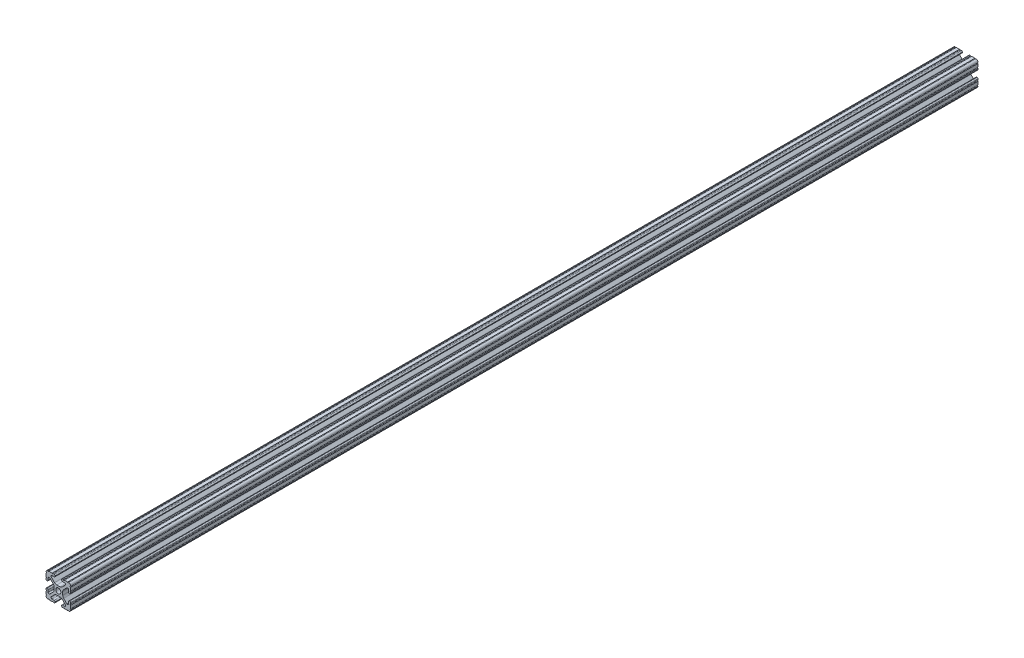
SolidWorks part; units mm, degrees
ref_plane "Front Plane" through (0, 0, 0) normal (0, 0, 1) x (1, 0, 0)
ref_plane "Top Plane" through (0, 0, 0) normal (0, 1, 0) x (1, 0, 0)
ref_plane "Right Plane" through (0, 0, 0) normal (1, 0, 0) x (0, 0, -1)
sketch "Sketch1" plane through (0, 0, 0) normal (0, 0, 1) x (1, 0, 0)
  line L88 (-7.1797, -8.6452) -> (-3.9523, -5.4237)
  line L89 (-1.7093, -4.4958) -> (1.7093, -4.4958)
  line L90 (3.9523, -5.4237) -> (7.1797, -8.6452)
  line L91 (6.4164, -10.4902) -> (4.2875, -10.4902)
  line L92 (3.2385, -11.5392) -> (3.2385, -11.651)
  line L93 (4.2875, -12.7) -> (5.3171, -12.7)
  line L94 (6.3331, -12.7) -> (9.5504, -12.7)
  line L95 (12.7, -9.5504) -> (12.7, -6.3331)
  line L96 (12.7, -5.3171) -> (12.7, -4.2875)
  line L97 (11.651, -3.2385) -> (11.5392, -3.2385)
  line L98 (10.4902, -4.2875) -> (10.4902, -6.4021)
  line L99 (8.7371, -7.1294) -> (5.441, -3.8408)
  line L100 (4.5085, -1.5932) -> (4.5085, 1.5932)
  line L101 (5.441, 3.8408) -> (8.7371, 7.1294)
  line L102 (10.4902, 6.4021) -> (10.4902, 4.2875)
  line L103 (11.5392, 3.2385) -> (11.651, 3.2385)
  line L104 (12.7, 4.2875) -> (12.7, 5.3171)
  line L105 (12.7, 6.3331) -> (12.7, 9.5504)
  line L106 (9.5504, 12.7) -> (6.3331, 12.7)
  line L107 (5.3171, 12.7) -> (4.2875, 12.7)
  line L108 (3.2385, 11.651) -> (3.2385, 11.5392)
  line L109 (4.2875, 10.4902) -> (6.4768, 10.4902)
  line L110 (7.207, 8.7244) -> (3.8983, 5.4232)
  line L111 (1.6558, 4.4958) -> (-1.6558, 4.4958)
  line L112 (-3.8983, 5.4232) -> (-7.207, 8.7244)
  line L113 (-6.4768, 10.4902) -> (-4.2875, 10.4902)
  line L114 (-3.2385, 11.5392) -> (-3.2385, 11.651)
  line L115 (-4.2875, 12.7) -> (-5.3171, 12.7)
  line L116 (-6.3331, 12.7) -> (-9.5504, 12.7)
  line L117 (-12.7, 9.5504) -> (-12.7, 6.3331)
  line L118 (-12.7, 5.3171) -> (-12.7, 4.2875)
  line L119 (-11.651, 3.2385) -> (-11.5392, 3.2385)
  line L120 (-10.4902, 4.2875) -> (-10.4902, 6.4021)
  line L121 (-8.7371, 7.1294) -> (-5.441, 3.8408)
  line L122 (-4.5085, 1.5932) -> (-4.5085, -1.5932)
  line L123 (-5.441, -3.8408) -> (-8.7371, -7.1294)
  line L124 (-10.4902, -6.4021) -> (-10.4902, -4.2875)
  line L125 (-11.5392, -3.2385) -> (-11.651, -3.2385)
  line L126 (-12.7, -4.2875) -> (-12.7, -5.3171)
  line L127 (-12.7, -6.3331) -> (-12.7, -9.5504)
  line L128 (-9.5504, -12.7) -> (-6.3331, -12.7)
  line L129 (-5.3171, -12.7) -> (-4.2875, -12.7)
  line L130 (-3.2385, -11.651) -> (-3.2385, -11.5392)
  line L131 (-4.2875, -10.4902) -> (-6.4164, -10.4902)
  circle A1 centre (0, 0) radius 2.6035
  arc A104 (-7.1797, -8.6452) -> (-6.4164, -10.4902) centre (-6.4164, -9.4098) ccw
  arc A105 (-1.7093, -4.4958) -> (-3.9523, -5.4237) centre (-1.7093, -7.6708) ccw
  arc A106 (3.9523, -5.4237) -> (1.7093, -4.4958) centre (1.7093, -7.6708) ccw
  arc A107 (6.4164, -10.4902) -> (7.1797, -8.6452) centre (6.4164, -9.4098) ccw
  arc A108 (4.2875, -10.4902) -> (3.2385, -11.5392) centre (4.2875, -11.5392) ccw
  arc A109 (3.2385, -11.651) -> (4.2875, -12.7) centre (4.2875, -11.651) ccw
  arc A110 (6.3331, -12.7) -> (5.3171, -12.7) centre (5.8251, -12.7) ccw
  arc A111 (10.5664, -12.6998) -> (9.5504, -12.7) centre (10.0584, -12.7) ccw
  arc A112 (10.5664, -12.6998) -> (12.6998, -10.5664) centre (10.5918, -10.5918) ccw
  arc A113 (12.7, -9.5504) -> (12.6998, -10.5664) centre (12.7, -10.0584) ccw
  arc A114 (12.7, -5.3171) -> (12.7, -6.3331) centre (12.7, -5.8251) ccw
  arc A115 (12.7, -4.2875) -> (11.651, -3.2385) centre (11.651, -4.2875) ccw
  arc A116 (11.5392, -3.2385) -> (10.4902, -4.2875) centre (11.5392, -4.2875) ccw
  arc A117 (8.7371, -7.1294) -> (10.4902, -6.4021) centre (9.4628, -6.4021) ccw
  arc A118 (4.5085, -1.5932) -> (5.441, -3.8408) centre (7.6835, -1.5932) ccw
  arc A119 (5.441, 3.8408) -> (4.5085, 1.5932) centre (7.6835, 1.5932) ccw
  arc A120 (10.4902, 6.4021) -> (8.7371, 7.1294) centre (9.4628, 6.4021) ccw
  arc A121 (10.4902, 4.2875) -> (11.5392, 3.2385) centre (11.5392, 4.2875) ccw
  arc A122 (11.651, 3.2385) -> (12.7, 4.2875) centre (11.651, 4.2875) ccw
  arc A123 (12.7, 6.3331) -> (12.7, 5.3171) centre (12.7, 5.8251) ccw
  arc A124 (12.6998, 10.5664) -> (12.7, 9.5504) centre (12.7, 10.0584) ccw
  arc A125 (12.6998, 10.5664) -> (10.5664, 12.6998) centre (10.5918, 10.5918) ccw
  arc A126 (9.5504, 12.7) -> (10.5664, 12.6998) centre (10.0584, 12.7) ccw
  arc A127 (5.3171, 12.7) -> (6.3331, 12.7) centre (5.8251, 12.7) ccw
  arc A128 (4.2875, 12.7) -> (3.2385, 11.651) centre (4.2875, 11.651) ccw
  arc A129 (3.2385, 11.5392) -> (4.2875, 10.4902) centre (4.2875, 11.5392) ccw
  arc A130 (7.207, 8.7244) -> (6.4768, 10.4902) centre (6.4768, 9.4563) ccw
  arc A131 (1.6558, 4.4958) -> (3.8983, 5.4232) centre (1.6558, 7.6708) ccw
  arc A132 (-3.8983, 5.4232) -> (-1.6558, 4.4958) centre (-1.6558, 7.6708) ccw
  arc A133 (-6.4768, 10.4902) -> (-7.207, 8.7244) centre (-6.4768, 9.4563) ccw
  arc A134 (-4.2875, 10.4902) -> (-3.2385, 11.5392) centre (-4.2875, 11.5392) ccw
  arc A135 (-3.2385, 11.651) -> (-4.2875, 12.7) centre (-4.2875, 11.651) ccw
  arc A136 (-6.3331, 12.7) -> (-5.3171, 12.7) centre (-5.8251, 12.7) ccw
  arc A137 (-10.5664, 12.6998) -> (-9.5504, 12.7) centre (-10.0584, 12.7) ccw
  arc A138 (-10.5664, 12.6998) -> (-12.6998, 10.5664) centre (-10.5918, 10.5918) ccw
  arc A139 (-12.7, 9.5504) -> (-12.6998, 10.5664) centre (-12.7, 10.0584) ccw
  arc A140 (-12.7, 5.3171) -> (-12.7, 6.3331) centre (-12.7, 5.8251) ccw
  arc A141 (-12.7, 4.2875) -> (-11.651, 3.2385) centre (-11.651, 4.2875) ccw
  arc A142 (-11.5392, 3.2385) -> (-10.4902, 4.2875) centre (-11.5392, 4.2875) ccw
  arc A143 (-8.7371, 7.1294) -> (-10.4902, 6.4021) centre (-9.4628, 6.4021) ccw
  arc A144 (-4.5085, 1.5932) -> (-5.441, 3.8408) centre (-7.6835, 1.5932) ccw
  arc A145 (-5.441, -3.8408) -> (-4.5085, -1.5932) centre (-7.6835, -1.5932) ccw
  arc A146 (-10.4902, -6.4021) -> (-8.7371, -7.1294) centre (-9.4628, -6.4021) ccw
  arc A147 (-10.4902, -4.2875) -> (-11.5392, -3.2385) centre (-11.5392, -4.2875) ccw
  arc A148 (-11.651, -3.2385) -> (-12.7, -4.2875) centre (-11.651, -4.2875) ccw
  arc A149 (-12.7, -6.3331) -> (-12.7, -5.3171) centre (-12.7, -5.8251) ccw
  arc A150 (-12.6998, -10.5664) -> (-12.7, -9.5504) centre (-12.7, -10.0584) ccw
  arc A151 (-12.6998, -10.5664) -> (-10.5664, -12.6998) centre (-10.5918, -10.5918) ccw
  arc A152 (-9.5504, -12.7) -> (-10.5664, -12.6998) centre (-10.0584, -12.7) ccw
  arc A153 (-5.3171, -12.7) -> (-6.3331, -12.7) centre (-5.8251, -12.7) ccw
  arc A154 (-4.2875, -12.7) -> (-3.2385, -11.651) centre (-4.2875, -11.651) ccw
  arc A155 (-3.2385, -11.5392) -> (-4.2875, -10.4902) centre (-4.2875, -11.5392) ccw
extrude "Boss-Extrude1" add sketch "Sketch1" along normal mid plane 933.45
sketch "Sketch2" plane through (4.5085, 0, 0) normal (1, 0, 0) x (0, 0, -1)
  line L0 (0, 0) -> (-393.7, 0) construction
  line L1 (-466.725, -1.5932) -> (-466.725, 1.5932) construction
  line L2 (0, 0) -> (0, 58.4486) construction
  line L3 (-466.725, 6.3331) -> (-466.725, 9.5504) construction
  circle A0 centre (-358.775, 0) radius 3.175
  circle A1 centre (358.775, 0) radius 3.175
  circle A2 centre (-85.725, 0) radius 3.175
  circle A3 centre (85.725, 0) radius 3.175
  dimension "D1" = 6.35
  dimension "D2" = 107.95
  dimension "D3" = 6.35
  dimension "D4" = 381
extrude "Cut-Extrude1" cut sketch "Sketch2" against normal through all both and the other way through all
